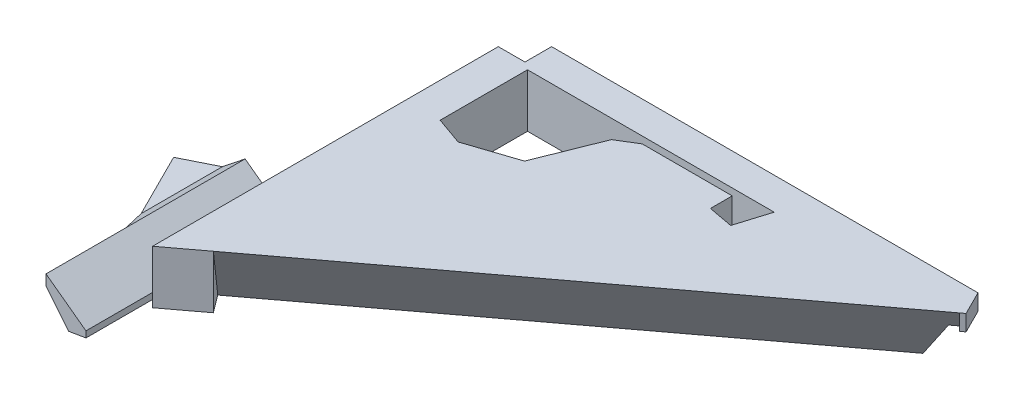
SolidWorks part; units mm, degrees
ref_plane "Front Plane" through (0, 0, 0) normal (0, 0, 1) x (1, 0, 0)
ref_plane "Top Plane" through (0, 0, 0) normal (0, 1, 0) x (1, 0, 0)
ref_plane "Right Plane" through (0, 0, 0) normal (1, 0, 0) x (0, 0, -1)
sketch "Sketch1" plane through (0, 0, 0) normal (0, 1, 0) x (1, 0, 0)
  line L0 (0, 0) -> (0, 101.6)
  line L1 (0, 101.6) -> (12.7, 101.6)
  line L2 (12.7, 101.6) -> (12.7, 114.3)
  line L3 (12.7, 114.3) -> (215.9, 114.3)
  line L4 (215.9, 114.3) -> (221.5796, 102.9408)
  line L5 (221.5796, 102.9408) -> (0, -63.1461)
  line L6 (0, -63.1461) -> (0, -94.8961)
  line L7 (0, -94.8961) -> (-19.05, -94.8961)
  line L8 (-19.05, -94.8961) -> (-19.05, -56.7961)
  line L9 (-19.05, -56.7961) -> (-41.7685, -11.3592)
  line L10 (-41.7685, -11.3592) -> (-19.05, 0)
  line L11 (-19.05, 0) -> (0, 0)
  line L12 (16.51, 99.0165) -> (16.51, 57.3807)
  line L13 (16.51, 99.0165) -> (134.0567, 99.0165)
  line L14 (74.4225, 95.7485) -> (117.3281, 95.7485)
  line L15 (74.4225, 95.7485) -> (65.3394, 90.1734)
  line L16 (65.3394, 90.1734) -> (53.4907, 60.6119)
  line L17 (117.3281, 95.7485) -> (117.3281, 85.3637)
  line L18 (16.51, 57.3807) -> (29.7614, 52.687)
  line L19 (29.7614, 52.687) -> (53.4907, 60.6119)
  line L20 (134.0567, 99.0165) -> (129.1902, 83.1589)
  line L21 (117.3281, 85.3637) -> (129.1902, 83.1589)
  point P15 (16.51, 57.3807)
  point P21 (29.7614, 52.687)
  point P24 (53.4907, 60.6119)
  dimension "D1" = 203.2
  dimension "D2" = 12.7
  dimension "D3" = 3.81
  dimension "D4" = 101.6
  dimension "D5" = 19.05
  dimension "D6" = 12.7
  dimension "D7" = 12.7
  dimension "D8" = 31.75
  dimension "D9" = 19.05
  dimension "D10" = 38.1
  dimension "D11" = 50.8
  dimension "D12" = 25.4
  dimension "D13" = 15.2835
extrude "Boss-Extrude1" add sketch "Sketch1" along normal blind 25.4
sketch "Sketch2" plane through (12.7, 0, 0) normal (-1, 0, 0) x (0, 0, 1)
  line L0 (-114.3, 25.4) -> (-114.3, 0) construction
  line L1 (-101.6, 0) -> (-114.3, 0)
  line L2 (-101.6, 0) -> (-101.6, 17.78)
  line L3 (-101.6, 17.78) -> (-114.3, 17.78)
  line L4 (-114.3, 0) -> (-114.3, 17.78)
  line L5 (-107.95, 17.78) -> (-107.95, 0) construction
  line L6 (-101.6, 8.89) -> (-114.3, 8.89) construction
  line L7 (-114.3, 25.4) -> (-101.6, 25.4) construction
  point P164 (-107.95, 8.89)
  dimension "D1" = 7.62
extrude "Cut-Extrude1" cut sketch "Sketch2" against normal through all
sketch "Sketch3" plane through (0, 0, 0) normal (0, 0, -1) x (-1, 0, 0)
  line L0 (0, 25.4) -> (0, 6.35)
  line L1 (0, 25.4) -> (0, 0) construction
  line L2 (0, 6.35) -> (19.05, 20.338)
  line L3 (19.05, 25.4) -> (0, 25.4)
  line L4 (0, 0) -> (19.05, 0) construction
  line L5 (19.05, 25.4) -> (19.05, 0) construction
  line L6 (19.05, 20.338) -> (26.2795, 15.3141)
  line L7 (26.2795, 15.3141) -> (41.7685, 15.3141)
  line L8 (41.7685, 25.4) -> (41.7685, 0) construction
  line L9 (41.7685, 15.3141) -> (41.7685, 25.4)
  line L10 (41.7685, 25.4) -> (19.05, 25.4)
  line L11 (41.7685, 10.7271) -> (26.2795, 10.7271)
  line L12 (26.2795, 10.7271) -> (19.05, 15.3141)
  line L13 (19.05, 15.3141) -> (8.2542, 2.0278)
  line L14 (8.2542, 2.0278) -> (0, 3.4097)
  line L15 (0, 25.4) -> (0, 0) construction
  line L16 (0, 3.4097) -> (0, 0)
  line L17 (0, 0) -> (41.7685, 0)
  line L18 (41.7685, 0) -> (41.7685, 10.7271)
  line L19 (41.7685, 10.7271) -> (41.6788, 10.8363)
  point P28 (8.0987, 0)
  point P30 (8.2542, 2.0278)
  line M2 (0, 0) -> (19.05, 0)
  line M3 (19.05, 0) -> (19.05, 25.4)
  line M4 (19.05, 25.4) -> (0, 25.4)
  line M5 (0, 25.4) -> (0, 0)
  dimension "D1" = 6.35
extrude "Cut-Extrude2" cut sketch "Sketch3" against normal through all contours L17 L18 L11 L12 M3 | L13 L14 M5 M2 M3 | L2 M5 M3 M4 | L9 L10 L6 L7 M3
ref_plane "Plane1" through (189.4857, 0, -142.0306) normal (0.8002, 0, -0.5998) x (0, 1, 0)
sketch "Sketch4" plane through (189.4857, 0, -142.0306) normal (0.8002, 0, -0.5998) x (0, 1, 0)
  line L0 (0, 40.0879) -> (25.4, 50.5276)
  line L1 (25.4, 50.5276) -> (0, 50.5276)
  line L2 (0, 50.5276) -> (0, 40.0879)
  point P2 (25.3027, 51.5319)
extrude "Cut-Extrude3" cut sketch "Sketch4" against normal blind 254
